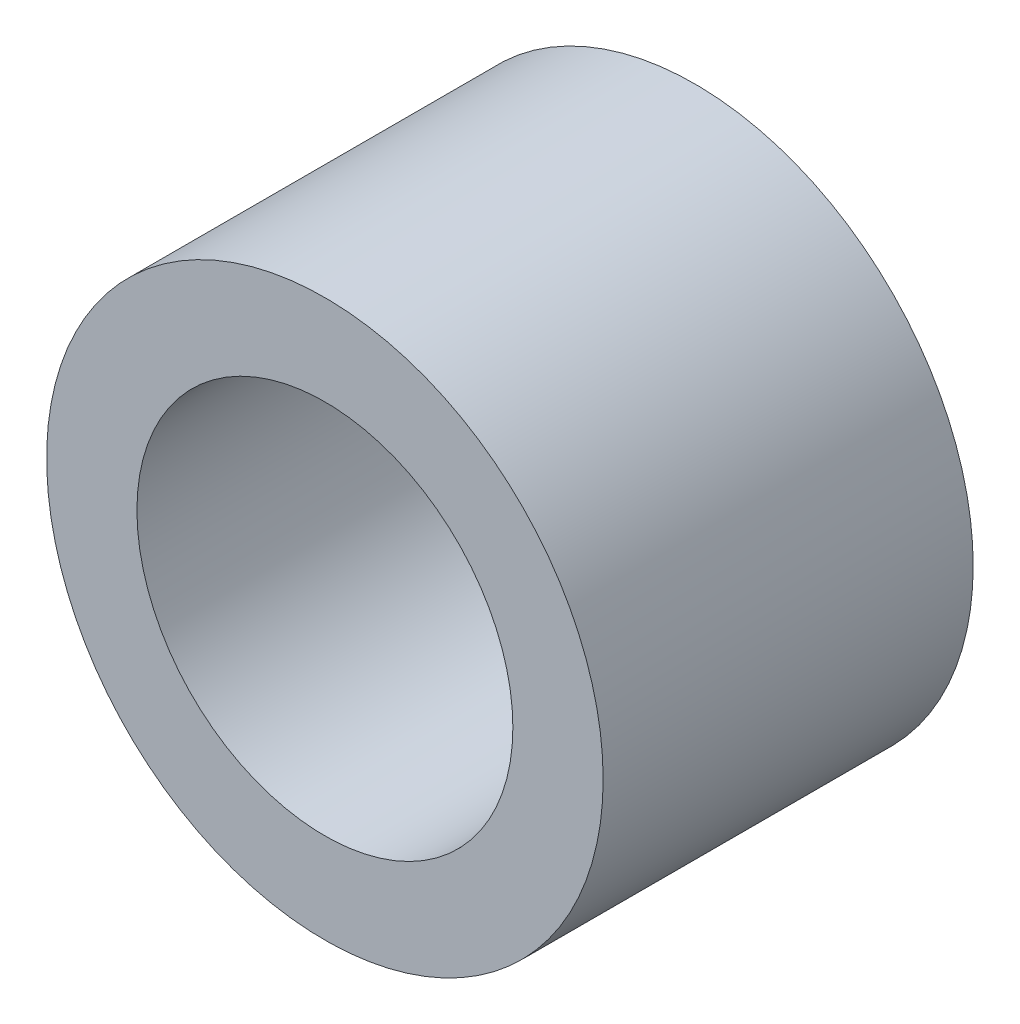
SolidWorks part; units mm, degrees
ref_plane "Front Plane" through (0, 0, 0) normal (0, 0, 1) x (1, 0, 0)
ref_plane "Top Plane" through (0, 0, 0) normal (0, 1, 0) x (1, 0, 0)
ref_plane "Right Plane" through (0, 0, 0) normal (1, 0, 0) x (0, 0, -1)
sketch "Sketch1" plane through (0, 0, 0) normal (0, 0, 1) x (1, 0, 0)
  circle A0 centre (0, 0) radius 4.7752
  circle A1 centre (0, 0) radius 3.2258
  dimension "D1" = 9.5504
  dimension "ID" = 6.4516
extrude "Extrude1" add sketch "Sketch1" along normal mid plane 6.35
sketch "Sketch2" plane through (0, 0, 0) normal (1, 0, 0) x (0, 0, -1)
  line L0 (-3.175, -3.2258) -> (3.175, -3.2258) construction
  line L3 (3.175, 3.2258) -> (-3.175, 3.2258) construction
  line L5 (-3.175, -3.2258) -> (3.175, -3.2258)
  line L6 (3.175, 3.2258) -> (-3.175, 3.2258)
sketch "Sketch4" plane through (0, 0, 3.175) normal (0, 0, 1) x (1, 0, 0)
  line L0 (0, 0) -> (-2.281, 2.281)
  line L1 (0, -6.985) -> (0, 6.985) construction
  circle A0 centre (0, 0) radius 3.2258 construction
  dimension "D1" = 45
